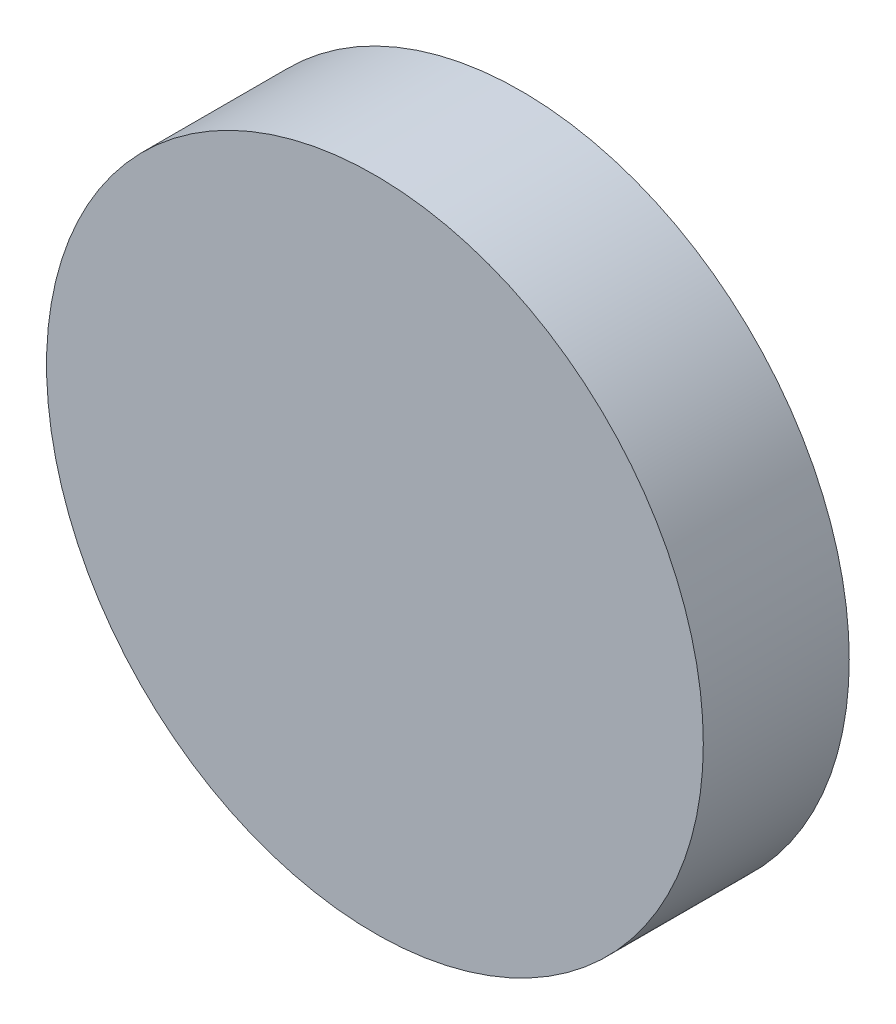
SolidWorks part; units mm, degrees
ref_plane "Front Plane" through (0, 0, 0) normal (0, 0, 1) x (1, 0, 0)
ref_plane "Top Plane" through (0, 0, 0) normal (0, 1, 0) x (1, 0, 0)
ref_plane "Right Plane" through (0, 0, 0) normal (1, 0, 0) x (0, 0, -1)
sketch "Sketch1" plane through (0, 0, 0) normal (0, 0, 1) x (1, 0, 0)
  circle A0 centre (0, 0) radius 13.5
  dimension "D1" = 27
extrude "Boss-Extrude1" add sketch "Sketch1" along normal blind 6
